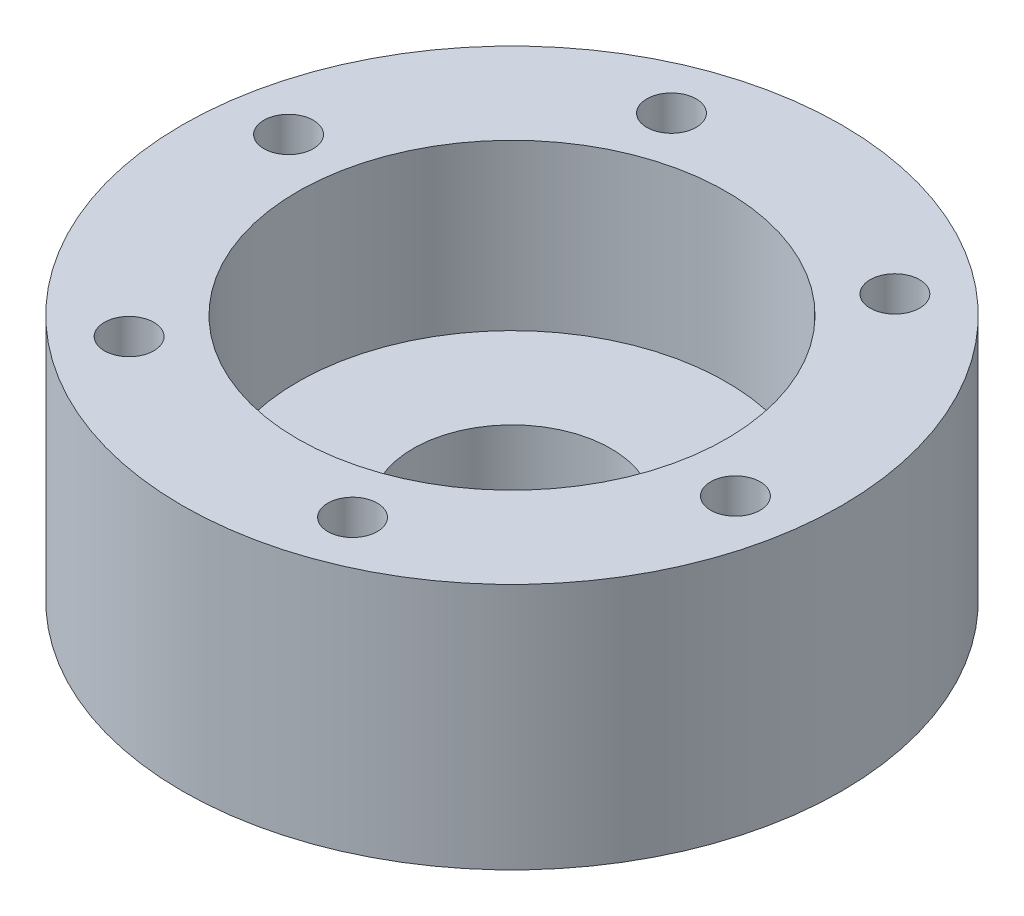
SolidWorks part; units mm, degrees
ref_plane "Front Plane" through (0, 0, 0) normal (0, 0, 1) x (1, 0, 0)
ref_plane "Top Plane" through (0, 0, 0) normal (0, 1, 0) x (1, 0, 0)
ref_plane "Right Plane" through (0, 0, 0) normal (1, 0, 0) x (0, 0, -1)
sketch "Sketch1" plane through (0, 0, 0) normal (0, 1, 0) x (1, 0, 0)
  circle A0 centre (0, 0) radius 20
  dimension "D1" = 40
extrude "Boss-Extrude1" add sketch "Sketch1" along normal blind 15
sketch "Sketch2" plane through (0, 15, 0) normal (0, 1, 0) x (1, 0, 0)
  circle A0 centre (0, 0) radius 13
  dimension "D1" = 26
extrude "Cut-Extrude1" cut sketch "Sketch2" against normal blind 10
sketch "Sketch3" plane through (0, 5, 0) normal (0, 1, 0) x (1, 0, 0)
  circle A0 centre (0, 0) radius 6
  dimension "D1" = 12
extrude "Cut-Extrude2" cut sketch "Sketch3" against normal blind 5
sketch "Sketch4" plane through (0, 15, 0) normal (0, 1, 0) x (1, 0, 0)
  circle A0 centre (-10.4931, -12.7336) radius 1.5
  circle A2 centre (-16.2742, 2.7205) radius 1.5
  circle A3 centre (-5.781, 15.4541) radius 1.5
  circle A4 centre (10.4931, 12.7336) radius 1.5
  circle A5 centre (16.2742, -2.7205) radius 1.5
  circle A6 centre (5.781, -15.4541) radius 1.5
  point P16 (0, 0)
  dimension "D2" = 3
  dimension "D3" = 6
  dimension "D1" = 16.5
extrude "Cut-Extrude3" cut sketch "Sketch4" against normal blind 15
